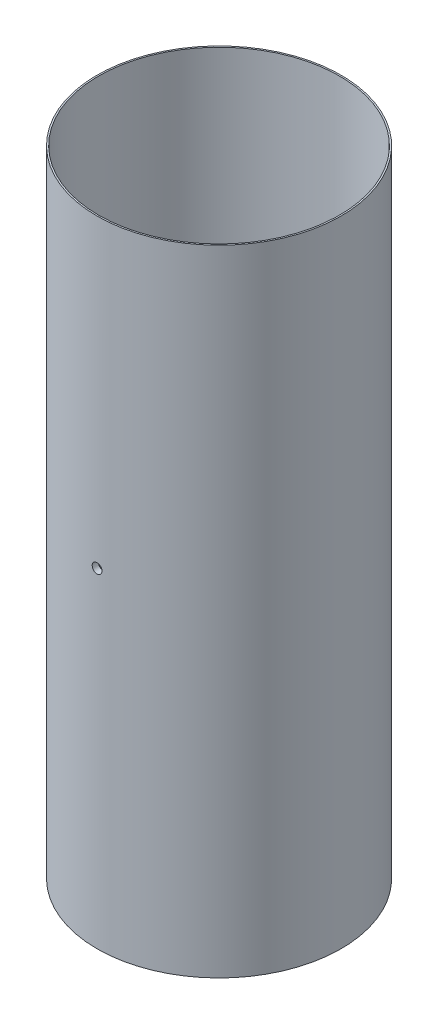
SolidWorks part; units mm, degrees
material "6061-T4 (SS)"
ref_plane "Front Plane" through (0, 0, 0) normal (0, 0, 1) x (1, 0, 0)
ref_plane "Top Plane" through (0, 0, 0) normal (0, 1, 0) x (1, 0, 0)
ref_plane "Right Plane" through (0, 0, 0) normal (1, 0, 0) x (0, 0, -1)
sketch "Sketch1" plane through (0, 0, 0) normal (0, 1, 0) x (1, 0, 0)
  circle A0 centre (0, 0) radius 63.5
  circle A1 centre (0, 0) radius 60.325
  dimension "D1" = 127
  dimension "D2" = 120.65
extrude "Boss-Extrude1" add sketch "Sketch1" along normal blind 330.2
sketch "Sketch5" plane through (0, 0, 0) normal (0, 1, 0) x (1, 0, 0)
  circle A0 centre (0, 0) radius 60.325
  circle A1 centre (0, 0) radius 62.7063
  dimension "D1" = 120.65
  dimension "D2" = 125.4125
extrude "Cut-Extrude1" cut sketch "Sketch5" along normal blind 158.75
sketch "Sketch6" plane through (0, 330.2, 0) normal (0, 1, 0) x (1, 0, 0)
  circle A0 centre (0, 0) radius 60.325
  circle A1 centre (0, 0) radius 62.7063
  dimension "D1" = 120.65
  dimension "D2" = 125.4125
extrude "Cut-Extrude2" cut sketch "Sketch6" against normal blind 120.65
ref_plane "Plane1" through (0, 0, 63.5) normal (0, 0, 1) x (1, 0, 0)
ref_plane "Plane2" through (0, 0, -63.5) normal (0, 0, 1) x (1, 0, 0)
sketch "Sketch8" plane through (0, 0, 63.5) normal (0, 0, 1) x (1, 0, 0)
  circle A0 centre (0, 171.45) radius 6.4556
  dimension "D1" = 171.45
sketch "Sketch12" plane through (0, 0, -63.5) normal (0, 0, 1) x (1, 0, 0)
  circle A0 centre (0, 171.45) radius 6.4556
hole_wizard "Tap Drill for 1/4-20 Tap8" positions "Sketch20" profile "Sketch19" hole size "1/4-20" standard "ANSI Inch"
sketch "Sketch20" plane through (0, 0, 63.5) normal (0, 0, 1) x (1, 0, 0)
  point P0 (0, 171.45)
sketch "Sketch19" plane through (0, 171.45, 63.5) normal (1, 0, 0) x (0, -1, 0)
  line L0 (0, 0) -> (0, 3.175)
  line L1 (0, 3.175) -> (2.5527, 3.175)
  line L2 (2.5527, 3.175) -> (2.5527, 0)
  line L5 (2.5527, 0) -> (0, 0)
  line L11 (0, -6.35) -> (0, 107.95) construction
  dimension "Thru Hole Dia." = 5.1054
  dimension "Thru Hole Depth" = 3.175
hole_wizard "Tap Drill for 1/4-20 Tap9" positions "Sketch21" profile "Sketch22" hole size "1/4-20" standard "ANSI Inch"
sketch "Sketch21" plane through (0, 0, -63.5) normal (0, 0, 1) x (1, 0, 0)
  point P0 (0, 171.45)
sketch "Sketch22" plane through (0, 171.45, -63.5) normal (1, 0, 0) x (0, 1, 0)
  line L0 (0, 0) -> (0, 3.175)
  line L1 (0, 3.175) -> (2.5527, 3.175)
  line L2 (2.5527, 3.175) -> (2.5527, 0)
  line L5 (2.5527, 0) -> (0, 0)
  line L11 (0, -6.35) -> (0, 107.95) construction
  dimension "Thru Hole Dia." = 5.1054
  dimension "Thru Hole Depth" = 3.175
ref_plane "Plane3" through (0, 313.5439, 0) normal (0, 1, 0) x (1, 0, 0)
sketch "Sketch24" plane through (0, 313.5439, 0) normal (0, 1, 0) x (1, 0, 0)
  circle A0 centre (0, 0) radius 60.325
sketch "Sketch25" plane through (0, 0, 0) normal (0, 0, 1) x (1, 0, 0)
  point P0 (0, 171.45)
  point P1 (0, 0)
sketch "Sketch28" plane through (0, 0, 0) normal (1, 0, 0) x (0, 0, -1)
  line L0 (0, 171.45) -> (-150.2291, 171.45) construction
  line L1 (-150.2291, 171.45) -> (0, 171.45) construction
  line L2 (0, 171.45) -> (137.0328, 171.45) construction
sketch "Sketch29" plane through (0, 0, 0) normal (0, 0, 1) x (1, 0, 0)
  line L0 (110.9363, 171.45) -> (-138.7821, 171.45) construction
ref_plane "Plane4" through (63.5, 0, 0) normal (1, 0, 0) x (0, 0, -1)
sketch "Sketch30" plane through (63.5, 0, 0) normal (1, 0, 0) x (0, 0, -1)
  line L0 (0, 364.0843) -> (0, -25.0636) construction
